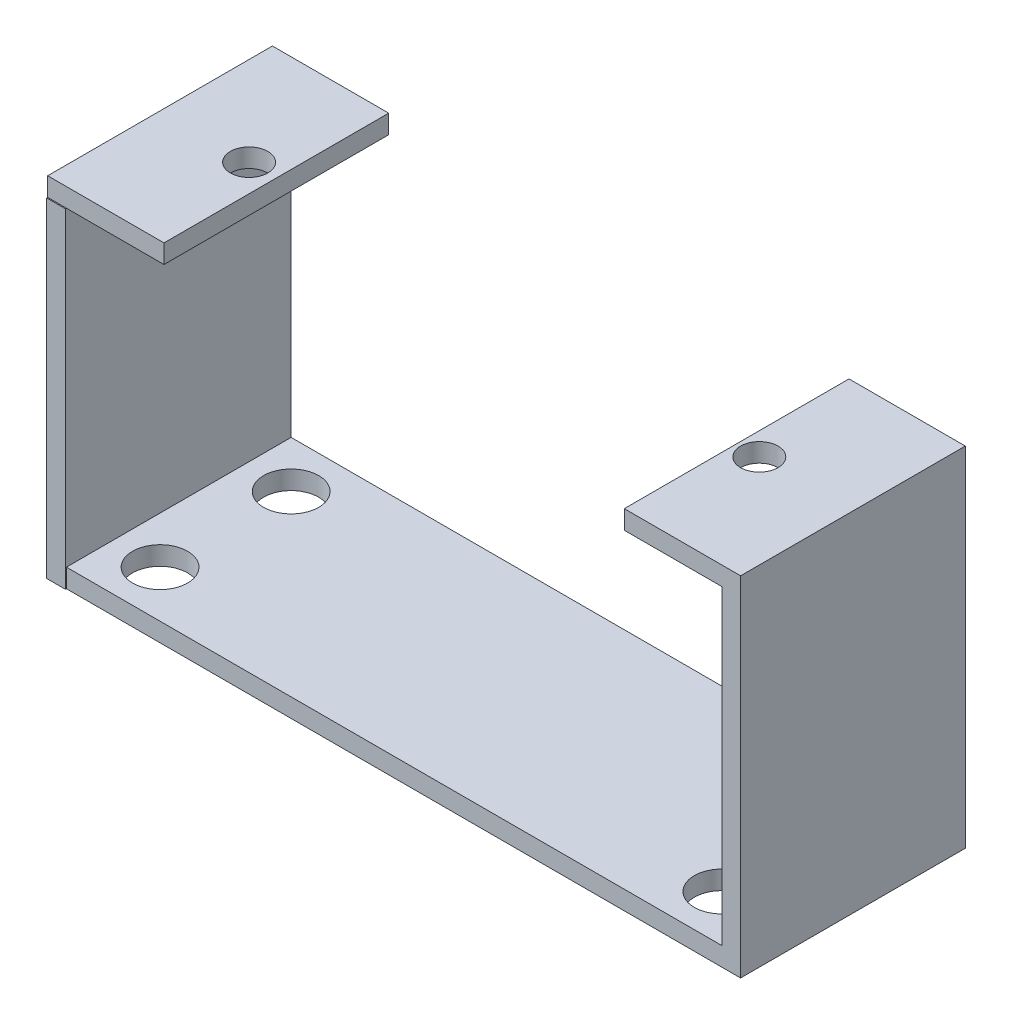
SolidWorks part; units mm, degrees
ref_plane "Front Plane" through (0, 0, 0) normal (0, 0, 1) x (1, 0, 0)
ref_plane "Top Plane" through (0, 0, 0) normal (0, 1, 0) x (1, 0, 0)
ref_plane "Right Plane" through (0, 0, 0) normal (1, 0, 0) x (0, 0, -1)
sketch "Sketch1" plane through (0, 0, 0) normal (0, 1, 0) x (1, 0, 0)
  line L1 (-17.3191, 3.438) -> (17.6809, 3.438)
  line L2 (-17.3191, 3.438) -> (-17.3191, -8.562)
  line L3 (-17.3191, -8.562) -> (17.6809, -8.562)
  line L4 (17.6809, 3.438) -> (17.6809, -8.562)
  dimension "D1" = 35
  dimension "D2" = 12
extrude "Boss-Extrude1" add sketch "Sketch1" along normal blind 1
sketch "Sketch2" plane through (-17.3191, 0, 0) normal (-1, 0, 0) x (0, 0, 1)
  line L1 (-3.438, 0) -> (8.6155, 0)
  line L2 (-3.438, 0) -> (-3.438, 17.6)
  line L3 (-3.438, 17.6) -> (8.6155, 17.6)
  line L4 (8.6155, 0) -> (8.6155, 17.6)
  dimension "D1" = 17.6
extrude "Boss-Extrude2" add sketch "Sketch2" along normal blind 1
sketch "Sketch3" plane through (17.6809, 0, 0) normal (1, 0, 0) x (0, 0, -1)
  line L1 (-8.562, 0) -> (3.438, 0)
  line L2 (-8.562, 0) -> (-8.562, 17.6)
  line L3 (-8.562, 17.6) -> (3.438, 17.6)
  line L4 (3.438, 0) -> (3.438, 17.6)
  dimension "D1" = 17.6
extrude "Boss-Extrude3" add sketch "Sketch3" along normal blind 1
sketch "Sketch5" plane through (0, 17.6, 0) normal (0, 1, 0) x (1, 0, 0)
  line L1 (18.6809, -8.562) -> (-18.3191, -8.562)
  line L2 (18.6809, -8.562) -> (18.6809, 3.438)
  line L3 (18.6809, 3.438) -> (-18.3191, 3.438)
  line L4 (-18.3191, -8.562) -> (-18.3191, 3.438)
extrude "Boss-Extrude4" add sketch "Sketch5" along normal blind 1
sketch "Sketch6" plane through (0, 18.6, 0) normal (0, 1, 0) x (1, 0, 0)
  line L0 (-18.3191, -8.562) -> (18.6809, -8.562) construction
  line L1 (12.4709, -8.562) -> (-12.1091, -8.562)
  line L2 (12.4709, -8.562) -> (12.4709, 3.438)
  line L3 (12.4709, 3.438) -> (-12.1091, 3.438)
  line L4 (-12.1091, -8.562) -> (-12.1091, 3.438)
  line L5 (18.6809, 3.438) -> (-18.3191, 3.438) construction
  line L6 (-18.3191, 3.438) -> (-18.3191, -8.562) construction
  dimension "D1" = 24.58
  dimension "D2" = 6.21
extrude "Cut-Extrude1" cut sketch "Sketch6" against normal blind 1
sketch "Sketch7" plane through (0, 18.6, 0) normal (0, 1, 0) x (1, 0, 0)
  line L0 (12.4709, -8.562) -> (18.6809, -8.562) construction
  line L3 (18.6809, -8.562) -> (18.6809, 3.438) construction
  circle A0 centre (13.6809, -2.562) radius 1
  dimension "D1" = 2
  dimension "D2" = 6
  dimension "D3" = 5
extrude "Cut-Extrude2" cut sketch "Sketch7" against normal blind 1
sketch "Sketch8" plane through (0, 18.6, 0) normal (0, 1, 0) x (1, 0, 0)
  circle A0 centre (-13.5691, -2.5587) radius 1
  circle A1 centre (13.6809, -2.562) radius 1 construction
  dimension "D1" = 2
  dimension "D2" = 27.25
extrude "Cut-Extrude3" cut sketch "Sketch8" against normal blind 1
sketch "Sketch9" plane through (0, 1, 0) normal (0, 1, 0) x (1, 0, 0)
  line L0 (17.6809, 3.438) -> (-17.3191, 3.438) construction
  line L1 (-17.3191, -8.562) -> (17.6809, -8.562) construction
  line L2 (17.6809, -8.562) -> (17.6809, 3.438) construction
  line L3 (-17.3191, 3.438) -> (-17.3191, -8.562) construction
  circle A0 centre (15.1809, 0.938) radius 1.47
  circle A1 centre (15.1809, -6.062) radius 1.47
  circle A2 centre (-14.8191, 0.938) radius 1.47
  circle A3 centre (-14.8191, -6.062) radius 1.47
  dimension "D1" = 2.94
  dimension "D2" = 2.94
  dimension "D3" = 2.5
  dimension "D4" = 2.5
  dimension "D7" = 2.94
  dimension "D8" = 2.94
  dimension "D9" = 2.5
  dimension "D10" = 2.5
  dimension "D11" = 2.5
  dimension "D12" = 2.5
  dimension "D5" = 2.5
  dimension "D6" = 2.5
extrude "Cut-Extrude4" cut sketch "Sketch9" against normal blind 10
